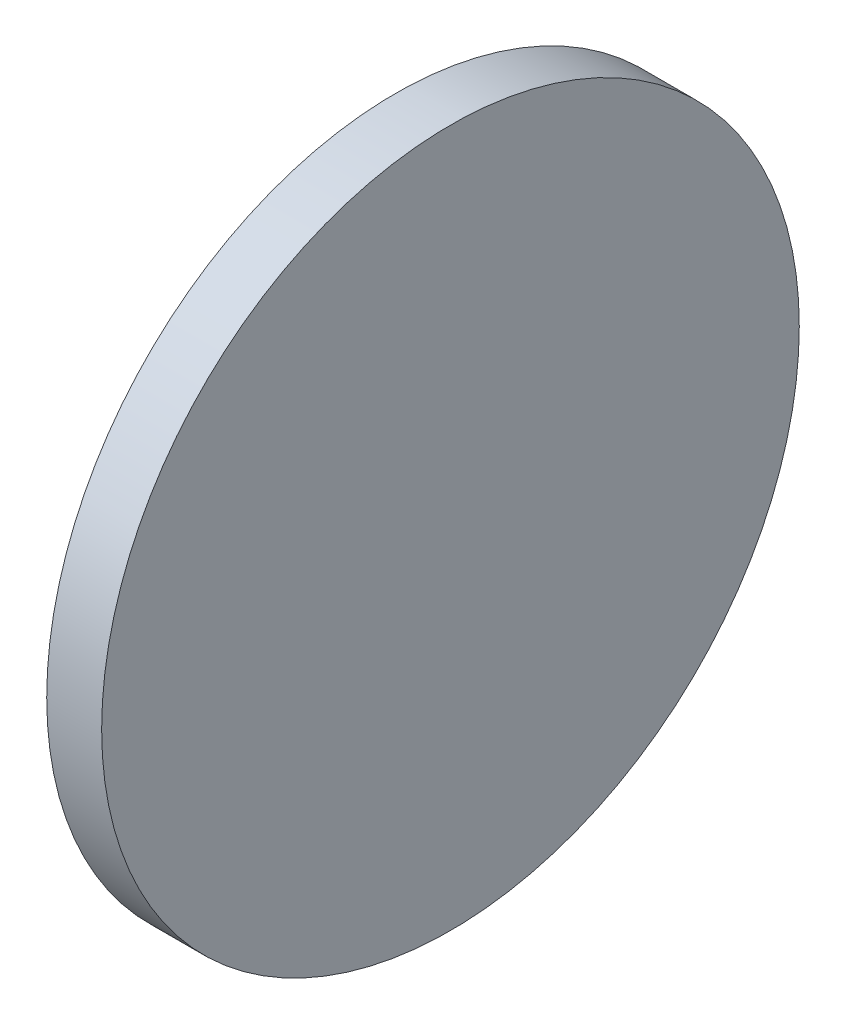
SolidWorks part; units mm, degrees
ref_plane "前视基准面" through (0, 0, 0) normal (0, 0, 1) x (1, 0, 0)
ref_plane "上视基准面" through (0, 0, 0) normal (0, 1, 0) x (1, 0, 0)
ref_plane "右视基准面" through (0, 0, 0) normal (1, 0, 0) x (0, 0, -1)
sketch "草图1" plane through (0, 0, 0) normal (0, 0, 1) x (1, 0, 0)
  line L0 (110.1654, 65.2336) -> (128.9614, 65.2336) construction
  line L1 (115.7646, 65.2336) -> (115.7646, 77.9336)
  line L2 (117.7646, 65.2336) -> (117.7646, 77.9336)
  line L3 (115.7646, 65.2336) -> (117.7646, 65.2336)
  line L5 (115.7646, 77.9336) -> (117.7646, 77.9336)
revolve "旋转1" add sketch "草图1" angle 360 about L0
